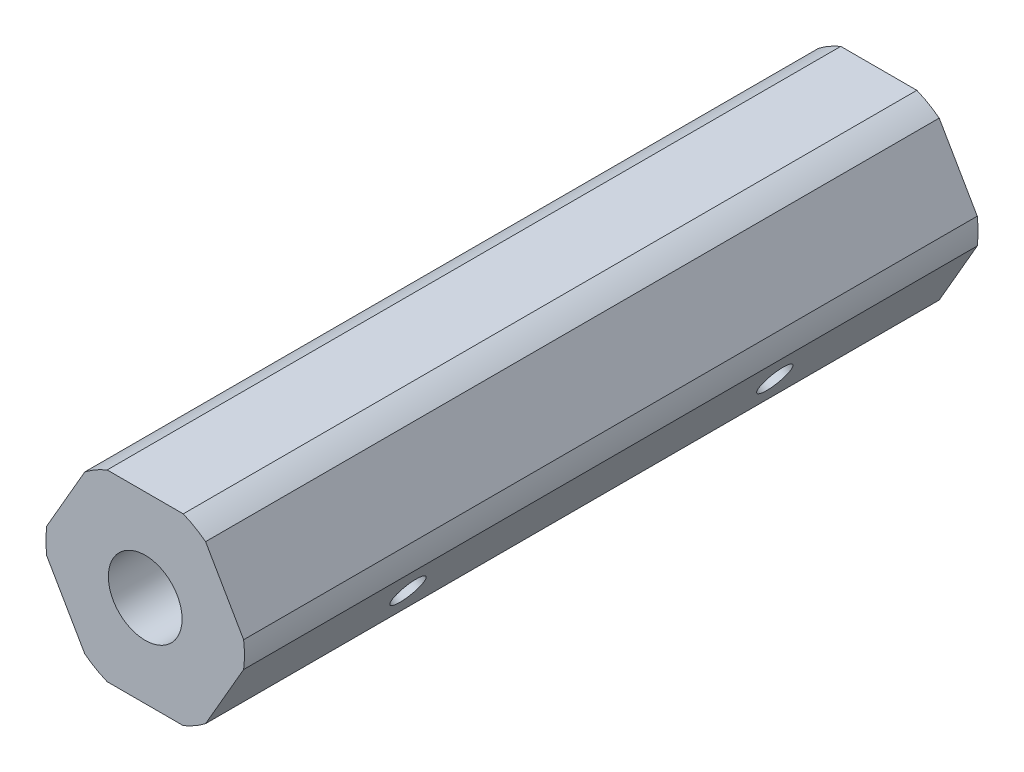
SolidWorks part; units mm, degrees
material "6061-T6 (SS)"
ref_plane "Front Plane" through (0, 0, 0) normal (0, 0, 1) x (1, 0, 0)
ref_plane "Top Plane" through (0, 0, 0) normal (0, 1, 0) x (1, 0, 0)
ref_plane "Right Plane" through (0, 0, 0) normal (1, 0, 0) x (0, 0, -1)
sketch "Sketch1" plane through (0, 0, 0) normal (0, 0, 1) x (1, 0, 0)
  line L1 (-2.635, -6.35) -> (2.635, -6.35)
  line L2 (4.1818, -5.457) -> (6.8168, -0.893)
  line L3 (6.8168, 0.893) -> (4.1818, 5.457)
  line L4 (2.635, 6.35) -> (-2.635, 6.35)
  line L5 (-4.1818, 5.457) -> (-6.8168, 0.893)
  line L6 (-6.8168, -0.893) -> (-4.1818, -5.457)
  circle A0 centre (0, 0) radius 6.35 construction
  arc A1 (-6.8168, 0.893) -> (-6.8168, -0.893) centre (0, 0) ccw
  arc A2 (-2.635, 6.35) -> (-4.1818, 5.457) centre (0, 0) ccw
  arc A3 (-4.1818, -5.457) -> (-2.635, -6.35) centre (0, 0) ccw
  arc A4 (2.635, -6.35) -> (4.1818, -5.457) centre (0, 0) ccw
  arc A5 (6.8168, -0.893) -> (6.8168, 0.893) centre (0, 0) ccw
  arc A6 (4.1818, 5.457) -> (2.635, 6.35) centre (0, 0) ccw
  dimension "D1" = 12.7
  dimension "D2" = 13.75
extrude "Boss-Extrude1" add sketch "Sketch1" along normal mid plane 50.8
hole_wizard "1/4-20 Tapped Hole1" positions "Sketch2" profile "Sketch3" tap size "1/4-20" standard "ANSI Inch" end condition through all
sketch "Sketch2" plane through (0, 0, 25.4) normal (0, 0, 1) x (1, 0, 0)
  point P0 (0, 0)
sketch "Sketch3" plane through (0, 0, 25.4) normal (1, 0, 0) x (0, -1, 0)
  line L0 (0, 0) -> (0, 50.8)
  line L1 (0, 50.8) -> (2.5527, 50.8)
  line L2 (2.5527, 50.8) -> (2.5527, 0)
  line L5 (2.5527, 0) -> (0, 0)
  line L11 (0, -6.35) -> (0, 107.95) construction
  dimension "Thru Tap Drill Dia." = 5.1054
  dimension "Thru Tap Drill Depth" = 50.8
cosmetic thread "Hole Thread1"
hole_wizard "#4-40 Tapped Hole1" positions "Sketch4" profile "Sketch5" tap size "#4-40" standard "ANSI Inch" end condition through all
sketch "Sketch4" plane through (0.7368, -11.4239, -31.75) normal (0.866, -0.5, 0) x (0, 0, -1)
  point P0 (-44.45, 120.65)
  point P3 (-19.05, 120.65)
  point P6 (-19.05, 9.525)
  point P9 (-44.45, 9.525)
sketch "Sketch5" plane through (61.0618, 93.0621, 12.7) normal (0, 0, 1) x (0.5, 0.866, 0)
  line L0 (0, 0) -> (0, 15.4789)
  line L1 (0, 15.4789) -> (1.1303, 15.4789)
  line L2 (1.1303, 15.4789) -> (1.1303, 0)
  line L3 (1.1303, 0) -> (0, 0)
  line L4 (0, -6.35) -> (0, 107.95) construction
  dimension "Thru Tap Drill Dia." = 2.2606
  dimension "Thru Tap Drill Depth" = 15.4789
cosmetic thread "Hole Thread2"
cosmetic thread "Hole Thread3"
hole_wizard "#4-40 Tapped Hole2" positions "Sketch6" profile "Sketch7" tap size "#4-40" standard "ANSI Inch" end condition through all
sketch "Sketch6" plane through (-54.8257, -107.661, -31.75) normal (0.866, -0.5, 0) x (0, 0, -1)
  point P0 (-44.45, 120.65)
  point P3 (-19.05, 120.65)
  point P6 (-19.05, 9.525)
  point P9 (-44.45, 9.525)
sketch "Sketch7" plane through (5.4993, -3.175, 12.7) normal (0, 0, 1) x (0.5, 0.866, 0)
  line L0 (0, 0) -> (0, 15.4789)
  line L1 (0, 15.4789) -> (1.1303, 15.4789)
  line L2 (1.1303, 15.4789) -> (1.1303, 0)
  line L3 (1.1303, 0) -> (0, 0)
  line L4 (0, -6.35) -> (0, 107.95) construction
  dimension "Thru Tap Drill Dia." = 2.2606
  dimension "Thru Tap Drill Depth" = 15.4789
